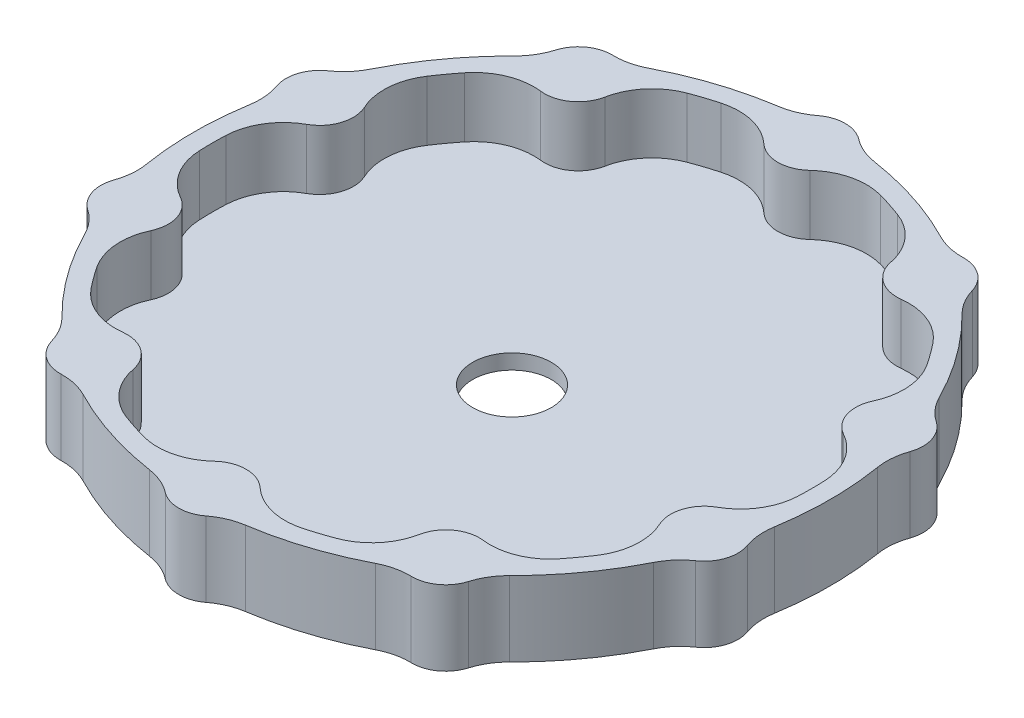
SolidWorks part; units mm, degrees
ref_plane "Front Plane" through (0, 0, 0) normal (0, 0, 1) x (1, 0, 0)
ref_plane "Top Plane" through (0, 0, 0) normal (0, 1, 0) x (1, 0, 0)
ref_plane "Right Plane" through (0, 0, 0) normal (1, 0, 0) x (0, 0, -1)
sketch "Sketch1" plane through (0, 0, 0) normal (0, 1, 0) x (1, 0, 0)
  circle A0 centre (0, 0) radius 42.5
  dimension "D1" = 85
extrude "Boss-Extrude1" add sketch "Sketch1" along normal blind 2
sketch "Sketch2" plane through (0, 0, 0) normal (0, 1, 0) x (1, 0, 0)
  circle A0 centre (0, 40) radius 5 construction
  circle A1 centre (0, 40) radius 4.5
  dimension "D2" = 10
  dimension "D3" = 0.5
  dimension "D1" = 40
extrude "Boss-Extrude2" add sketch "Sketch2" along normal offset from surface (10 mm away) 8 up to face at (0, 2, 42.5) offset beyond the face yes
sketch "Sketch3" plane through (0, 2, 0) normal (0, 1, 0) x (1, 0, 0)
  line L0 (-970.5909, 45) -> (49029.4091, 45) construction
  line L1 (-960.8113, 40) -> (49039.1887, 40) construction
  line L2 (-945.9172, 40) -> (49054.0828, 40) construction
  circle A0 centre (0, 0) radius 42.5
  circle A1 centre (0, 0) radius 40
  circle A2 centre (0, 40) radius 4.5 construction
  arc A4 (-3.8528, 42.325) -> (3.8528, 42.325) centre (0, 0) ccw construction
  circle A5 centre (0, 40) radius 5 construction
  point P12 (0, 40)
  point P17 (0, 0)
  point P18 (0, 0)
  dimension "D1" = 0
sketch "Sketch4" plane through (0, 2, 0) normal (0, 1, 0) x (1, 0, 0)
  circle A0 centre (0, 0) radius 5.25
  dimension "D1" = 10.5
extrude "Cut-Extrude1" cut sketch "Sketch4" against normal through all
extrude "Boss-Extrude4" add sketch "Sketch3" along normal up to surface (8 mm away) up to face at (0, 10, -35.5)
fillet "Fillet1" radius 8 4 edges at (3.8528, 5, -42.325) (-3.8528, 5, -42.325) (-4.4929, 6, -39.7469) (4.4929, 6, -39.7469)
pattern_circular "CirPattern2" count 10 over 360 about axis through (0, 0, 0) along (0, 1, 0) of "Boss-Extrude2", "Fillet1"
sketch "Sketch5" plane through (0, 0, 0) normal (0, 1, 0) x (1, 0, 0)
  circle A0 centre (0, -40) radius 5 construction
  circle A1 centre (0, 40) radius 5 construction
